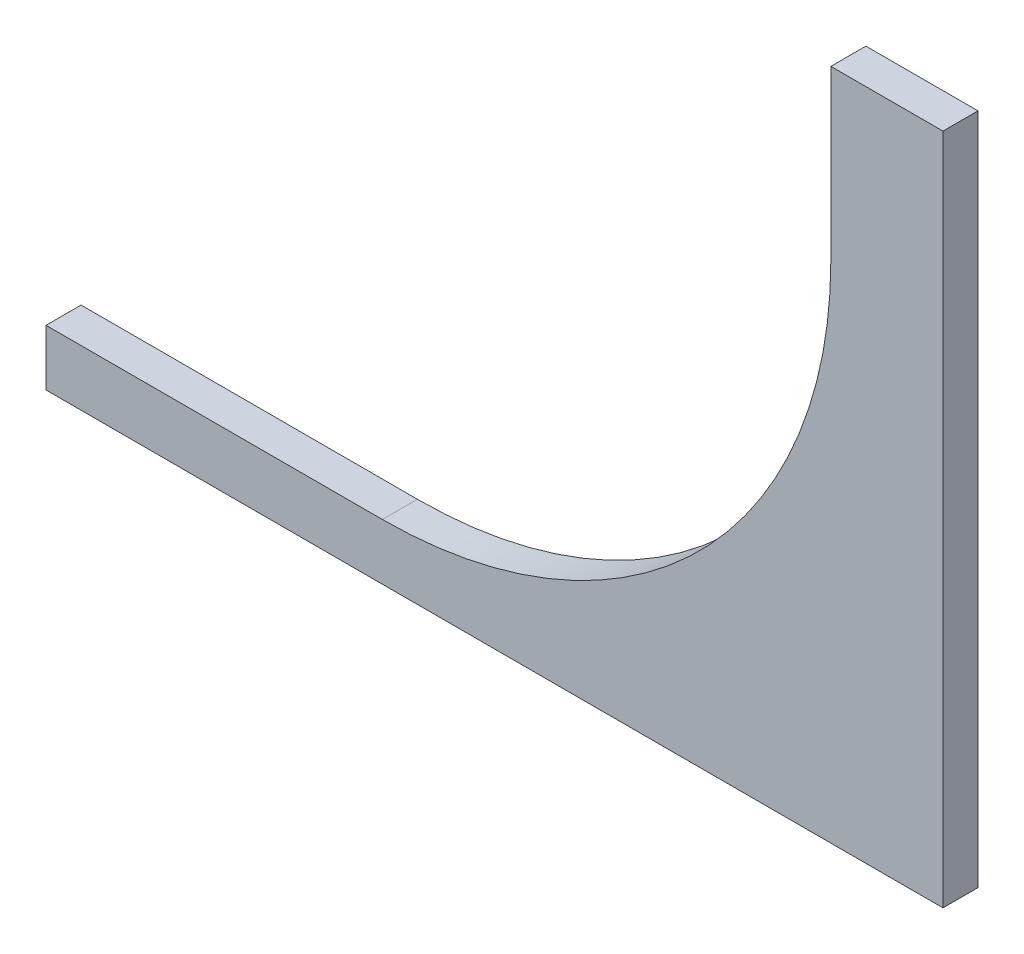
SolidWorks part; units mm, degrees
ref_plane "Front Plane" through (0, 0, 0) normal (0, 0, 1) x (1, 0, 0)
ref_plane "Top Plane" through (0, 0, 0) normal (0, 1, 0) x (1, 0, 0)
ref_plane "Right Plane" through (0, 0, 0) normal (1, 0, 0) x (0, 0, -1)
sketch "Sketch1" plane through (0, 0, 0) normal (0, 0, 1) x (1, 0, 0)
  line L1 (0, 0) -> (406.4, 0)
  line L2 (0, 0) -> (0, 304.8)
  line L3 (0, 304.8) -> (406.4, 304.8)
  line L4 (406.4, 0) -> (406.4, 304.8)
  dimension "D1" = 304.8
  dimension "D2" = 406.4
extrude "Boss-Extrude1" add sketch "Sketch1" along normal blind 15.875
sketch "Sketch2" plane through (0, 0, 15.875) normal (0, 0, 1) x (1, 0, 0)
  line L0 (0, 0) -> (406.4, 0) construction
  line L2 (0, 304.8) -> (0, 0) construction
  circle A0 centre (152.4, 228.6) radius 9.525
  dimension "D1" = 228.6
  dimension "D2" = 152.4
extrude "Cut-Extrude1" cut sketch "Sketch2" against normal through all
sketch "Sketch3" plane through (0, 0, 15.875) normal (0, 0, 1) x (1, 0, 0)
  line L0 (152.4, 228.6) -> (355.6, 228.6) construction
  line L1 (152.4, 228.6) -> (152.4, 25.4) construction
  line L2 (152.4, 25.4) -> (0, 25.4)
  line L3 (0, 304.8) -> (0, 0) construction
  line L4 (355.6, 228.6) -> (355.6, 304.8)
  line L5 (406.4, 304.8) -> (0, 304.8) construction
  line L6 (0, 25.4) -> (0, 304.8)
  line L7 (355.6, 304.8) -> (0, 304.8)
  arc A0 (152.4, 25.4) -> (355.6, 228.6) centre (152.4, 228.6) ccw
extrude "Cut-Extrude2" cut sketch "Sketch3" against normal through all
sketch "Sketch4" plane through (0, 0, 0) normal (0, 0, 1) x (1, 0, 0)
  circle A0 centre (152.4, 228.6) radius 152.4
  dimension "D1" = 304.8
